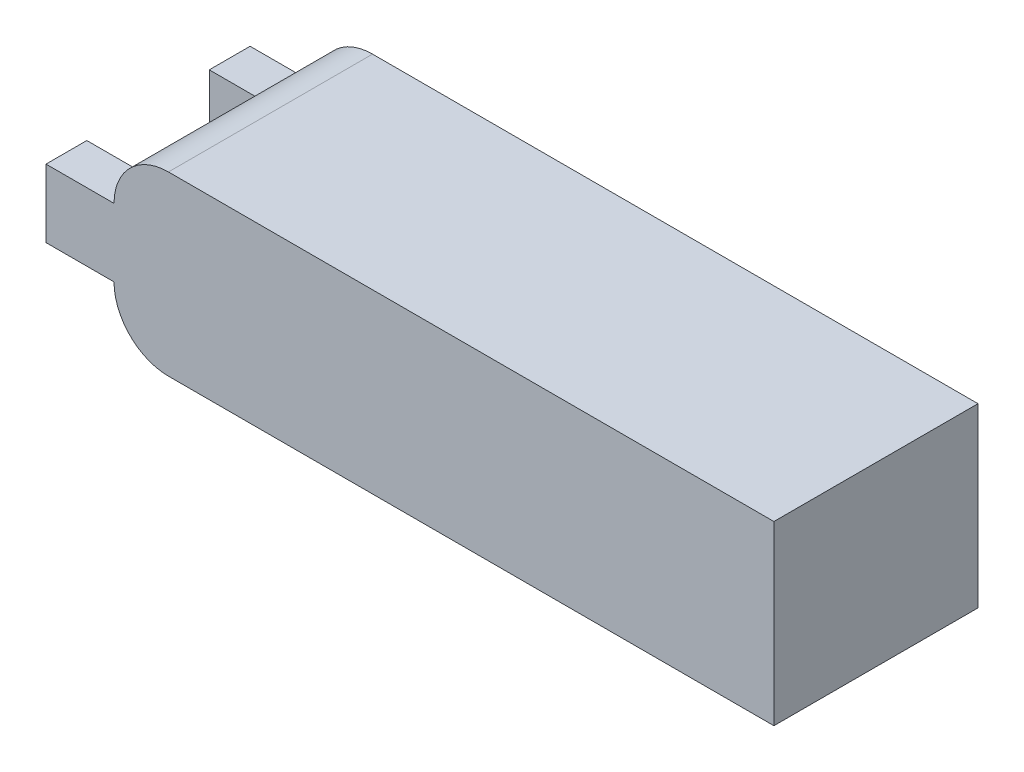
SolidWorks part; units mm, degrees
ref_plane "Front Plane" through (0, 0, 0) normal (0, 0, 1) x (1, 0, 0)
ref_plane "Top Plane" through (0, 0, 0) normal (0, 1, 0) x (1, 0, 0)
ref_plane "Right Plane" through (0, 0, 0) normal (1, 0, 0) x (0, 0, -1)
sketch "Sketch1" plane through (0, 0, 0) normal (0, 1, 0) x (1, 0, 0)
  line L1 (0, 0) -> (97, 0)
  line L2 (0, 0) -> (0, 30)
  line L3 (0, 30) -> (97, 30)
  line L4 (97, 0) -> (97, 30)
  dimension "D1" = 97
  dimension "D2" = 30
extrude "Boss-Extrude1" add sketch "Sketch1" along normal blind 26
fillet "Fillet1" radius 8 2 edges at (0, 0, -15) (0, 26, -15)
sketch "Sketch2" plane through (0, 0, 0) normal (-1, 0, 0) x (0, 0, 1)
  line L0 (-30, 8) -> (0, 8) construction
  line L1 (-30, 18) -> (-24, 18)
  line L2 (-30, 18) -> (-30, 8)
  line L3 (-30, 8) -> (-24, 8)
  line L4 (-24, 18) -> (-24, 8)
  line L6 (0, 18) -> (-6, 18)
  line L7 (0, 18) -> (0, 8)
  line L8 (0, 8) -> (-6, 8)
  line L9 (-6, 18) -> (-6, 8)
  dimension "D1" = 6
extrude "Boss-Extrude2" add sketch "Sketch2" along normal blind 10
